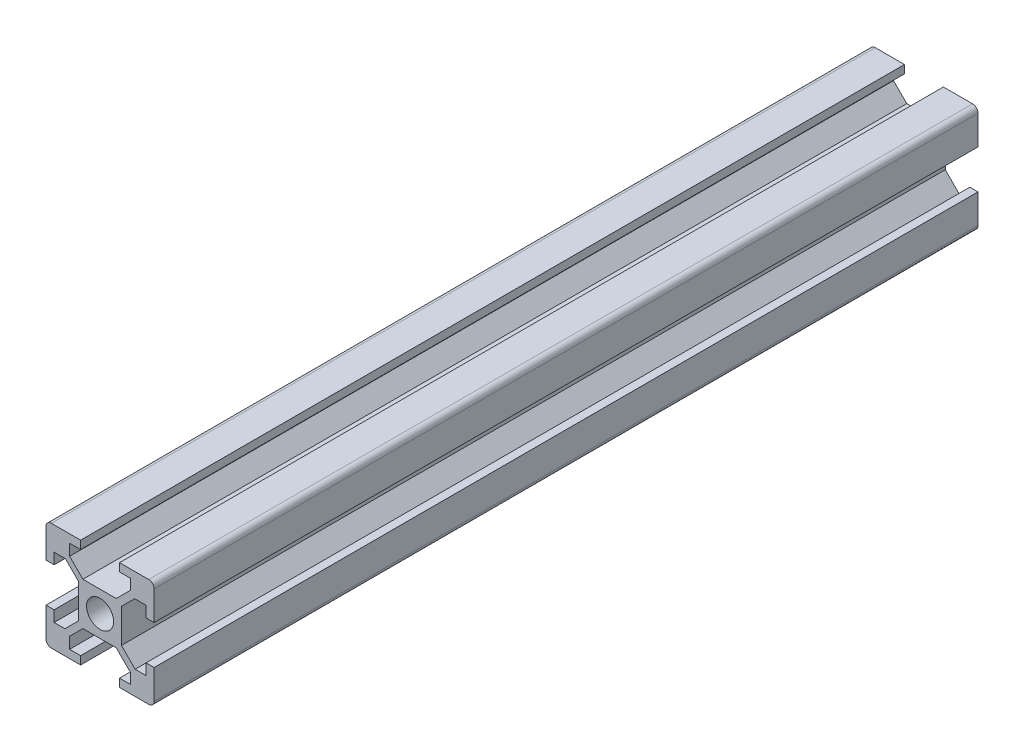
SolidWorks part; units mm, degrees
ref_plane "Front Plane" through (0, 0, 0) normal (0, 0, 1) x (1, 0, 0)
ref_plane "Top Plane" through (0, 0, 0) normal (0, 1, 0) x (1, 0, 0)
ref_plane "Right Plane" through (0, 0, 0) normal (1, 0, 0) x (0, 0, -1)
sketch "Sketch1" plane through (0, 0, 0) normal (0, 0, 1) x (1, 0, 0)
  line L0 (-9, -10) -> (-3.6, -10) construction
  line L1 (-9, 10) -> (-3.6, 10)
  line L2 (-10, 9) -> (-10, 3.6)
  line L3 (3.6, -10) -> (9, -10)
  line L4 (10, 9) -> (10, 3.6)
  line L7 (-3.178, 3.95) -> (2.9913, 3.95)
  line L8 (-3.95, 3.178) -> (-3.95, -3.0886)
  line L9 (-3.178, -3.95) -> (2.9913, -3.95)
  line L10 (3.95, 3.178) -> (3.95, -3.0886)
  line L13 (9, -10) -> (3.6, -10) construction
  line L14 (10, 9) -> (10, 3.6)
  line L15 (10, -9) -> (10, -3.6)
  line L16 (-10, -9) -> (-10, -3.6)
  line L17 (-10, 9) -> (-10, 3.6)
  line L18 (-9, 10) -> (-3.6, 10)
  line L19 (9, 10) -> (3.6, 10)
  line L20 (3.6, 10) -> (9, 10)
  line L21 (-10, -3.6) -> (-10, -9)
  line L22 (10, -3.6) -> (10, -9)
  line L23 (-3.6, -10) -> (-9, -10)
  line L24 (-5.63, 6.402) -> (-3.178, 3.95)
  line L25 (-9, 10) -> (-5.63, 10)
  line L26 (-10, 9) -> (-10, 5.63)
  line L27 (-8.5, 5.63) -> (-6.402, 5.63)
  line L28 (-5.63, 8.5) -> (-5.63, 6.402)
  line L29 (9, 10) -> (5.63, 10)
  line L30 (10, 9) -> (10, 5.63)
  line L31 (8.5, 5.63) -> (6.402, 5.63)
  line L32 (5.63, 8.5) -> (5.63, 6.5887)
  line L33 (-9, -10) -> (-5.63, -10)
  line L34 (-10, -9) -> (-10, -5.63)
  line L35 (-8.5, -5.63) -> (-6.4914, -5.63)
  line L36 (-5.63, -8.5) -> (-5.63, -6.402)
  line L37 (9, -10) -> (5.63, -10)
  line L38 (10, -9) -> (10, -5.63)
  line L39 (8.5, -5.63) -> (6.4914, -5.63)
  line L40 (5.63, -8.5) -> (5.63, -6.5887)
  line L41 (-5.63, 10) -> (-3.6, 10)
  line L43 (-5.63, 8.5) -> (-3.6, 8.5)
  line L44 (-3.6, 10) -> (-3.6, 8.5)
  line L45 (-10, 3.6) -> (-8.5, 3.6)
  line L46 (-10, 3.6) -> (-10, 5.63)
  line L48 (-8.5, 3.6) -> (-8.5, 5.63)
  line L49 (-10, -3.6) -> (-8.5, -3.6)
  line L50 (-10, -3.6) -> (-10, -5.63)
  line L52 (-8.5, -3.6) -> (-8.5, -5.63)
  line L53 (-5.63, -10) -> (-3.6, -10)
  line L55 (-5.63, -8.5) -> (-3.6, -8.5)
  line L56 (-3.6, -10) -> (-3.6, -8.5)
  line L57 (3.6, -10) -> (5.63, -10)
  line L58 (3.6, -10) -> (3.6, -8.5)
  line L59 (3.6, -8.5) -> (5.63, -8.5)
  line L61 (10, -3.6) -> (8.5, -3.6)
  line L62 (10, -3.6) -> (10, -5.63)
  line L64 (8.5, -3.6) -> (8.5, -5.63)
  line L65 (10, 3.6) -> (8.5, 3.6)
  line L66 (10, 3.6) -> (10, 5.63)
  line L68 (8.5, 3.6) -> (8.5, 5.63)
  line L69 (3.6, 10) -> (5.63, 10)
  line L70 (3.6, 10) -> (3.6, 8.5)
  line L71 (3.6, 8.5) -> (5.63, 8.5)
  line L73 (-6.402, 5.63) -> (-3.95, 3.178)
  line L74 (2.9913, 3.95) -> (5.63, 6.5887)
  line L75 (3.95, 3.178) -> (6.402, 5.63)
  line L76 (3.95, -3.0886) -> (6.4914, -5.63)
  line L77 (2.9913, -3.95) -> (5.63, -6.5887)
  line L78 (-3.95, -3.0886) -> (-6.4914, -5.63)
  line L79 (-3.178, -3.95) -> (-5.63, -6.402)
  circle A0 centre (0, 0) radius 2.5
  arc A1 (10, 9) -> (9, 10) centre (9, 9) ccw
  arc A2 (10, -9) -> (9, -10) centre (9, -9) cw
  arc A3 (-9, -10) -> (-10, -9) centre (-9, -9) cw
  arc A4 (-10, 9) -> (-9, 10) centre (-9, 9) cw
  point P0 (0, 0)
  dimension "D3" = 5
  dimension "D4" = 1
  dimension "D5" = 1
  dimension "D15" = 1.5
  dimension "D16" = 1.5
  dimension "D17" = 1.5
  dimension "D18" = 1.5
  dimension "D19" = 1.5
  dimension "D20" = 1.5
  dimension "D21" = 1.5
  dimension "D22" = 1.5
extrude "Boss-Extrude1" add sketch "Sketch1" along normal blind 482.6 contours A4 L2 L17 L45 L48 L27 L73 L8 L78 L35 L52 L49 L21 L16 A3 L23 L56 L55 L36 L79 L9 L77 L40 L59 L58 L3 A2 L15 L22 L61 L64 L39 L76 L10 L75 L31 L68 L65 L14 L4 A1 L19 L20 L70 L71 L32 L74 L7 L24
sketch "Sketch2" plane through (0, 10, 0) normal (0, 1, 0) x (1, 0, 0)
  line L1 (-16.6059, 0) -> (15.4945, 0) construction
  line L2 (-16.6059, 0) -> (-16.6059, -152.4) construction
  line L3 (-16.6059, -152.4) -> (15.4945, -152.4) construction
  line L4 (15.4945, 0) -> (15.4945, -152.4) construction
  line L5 (-16.6059, -152.4) -> (44.7556, -152.4)
  line L6 (-16.6059, -152.4) -> (-16.6059, -532.6547)
  line L7 (-16.6059, -532.6547) -> (44.7556, -532.6547)
  line L8 (44.7556, -152.4) -> (44.7556, -532.6547)
  dimension "D1" = 152.4
extrude "Cut-Extrude1" cut sketch "Sketch2" against normal through all
